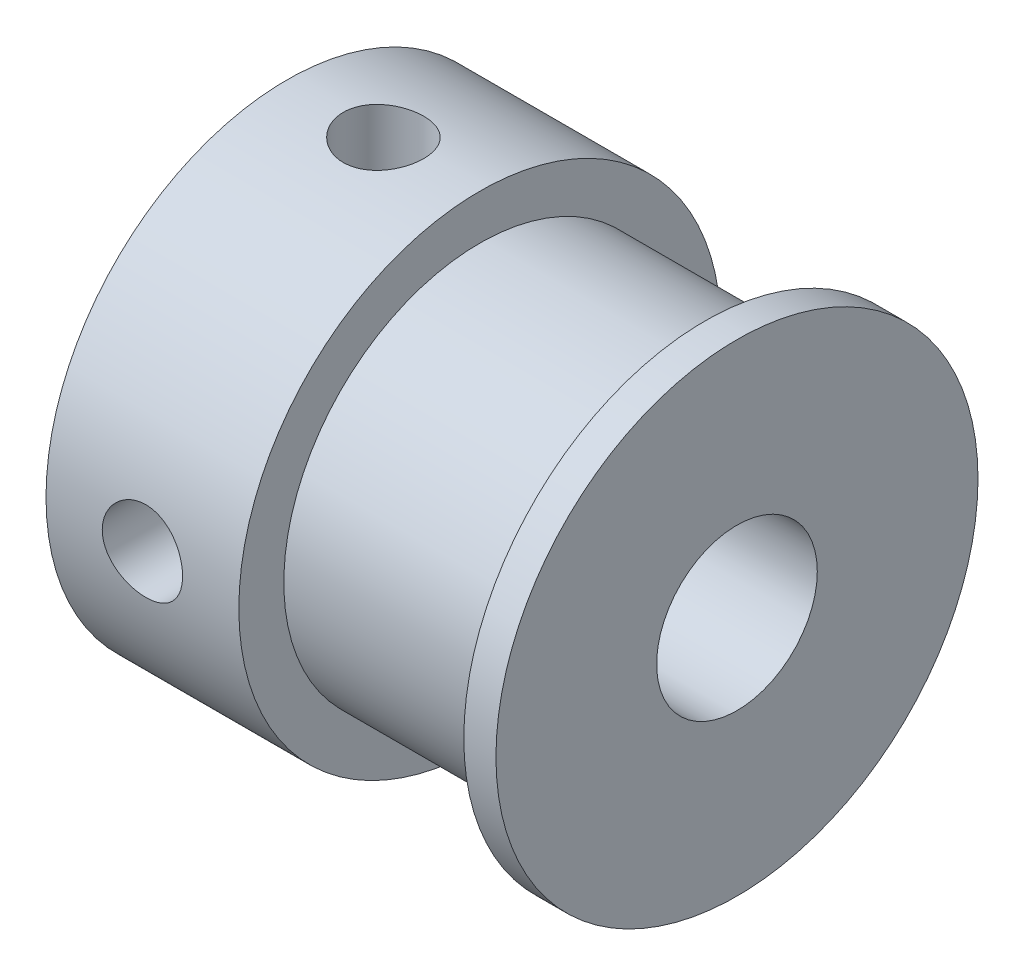
SolidWorks part; units mm, degrees
material "6061-T6 (SS)"
ref_plane "Front Plane" through (0, 0, 0) normal (0, 0, 1) x (1, 0, 0)
ref_plane "Top Plane" through (0, 0, 0) normal (0, 1, 0) x (1, 0, 0)
ref_plane "Right Plane" through (0, 0, 0) normal (1, 0, 0) x (0, 0, -1)
sketch "Sketch1" plane through (0, 0, 0) normal (0, 0, 1) x (1, 0, 0)
  line L0 (0, 2.5) -> (0, 7.5)
  line L1 (0, 7.5) -> (6, 7.5)
  line L2 (6, 7.5) -> (6, 6.1)
  line L3 (6, 6.1) -> (13, 6.1)
  line L4 (13, 6.1) -> (13, 7.5)
  line L5 (13, 7.5) -> (14, 7.5)
  line L6 (14, 7.5) -> (14, 2.5)
  line L7 (14, 2.5) -> (0, 2.5)
  line L8 (0, 0) -> (-7.6744, 0) construction
  dimension "D1" = 5
  dimension "D2" = 15
  dimension "D3" = 12.2
  dimension "D4" = 6
  dimension "D5" = 14
  dimension "D6" = 1
revolve "Revolve1" add sketch "Sketch1" angle 360 about L8
hole_wizard "M3x0.5 Tapped Hole1" positions "Sketch3" profile "Sketch2" tap size "M3x0.5" standard "ANSI Metric"
sketch "Sketch3" plane through (0, 0, 0) normal (0, 1, 0) x (1, 0, 0)
  line L0 (0, 0) -> (6, 0) construction
  line L1 (6, -6.1) -> (6, 6.1) construction
  point P8 (3, 0)
sketch "Sketch2" plane through (3, 0, 0) normal (1, 0, 0) x (0, 0, -1)
  line L0 (0, 0) -> (0, 7.5)
  line L1 (0, 7.5) -> (1.25, 7.5)
  line L2 (1.25, 7.5) -> (1.25, 0)
  line L5 (1.25, 0) -> (0, 0)
  line L11 (0, -6.35) -> (0, 107.95) construction
  dimension "Thread Major Dia." = 2.5
  dimension "Thru Tap Drill Depth" = 7.5
hole_wizard "M3x0.5 Tapped Hole2" positions "Sketch5" profile "Sketch4" tap size "M3x0.5" standard "ANSI Metric"
sketch "Sketch5" plane through (0, 0, 0) normal (0, 0, 1) x (1, 0, 0)
  line L0 (0, 0) -> (6, 0) construction
  line L1 (6, -6.1) -> (6, 6.1) construction
  point P7 (3, 0)
sketch "Sketch4" plane through (3, 0, 0) normal (1, 0, 0) x (0, 1, 0)
  line L0 (0, 0) -> (0, 7.5)
  line L1 (0, 7.5) -> (1.25, 7.5)
  line L2 (1.25, 7.5) -> (1.25, 0)
  line L5 (1.25, 0) -> (0, 0)
  line L11 (0, -6.35) -> (0, 107.95) construction
  dimension "Thread Major Dia." = 2.5
  dimension "Thru Tap Drill Depth" = 7.5
ref_plane "Plane1" through (9.5, 0, 0) normal (1, 0, 0) x (0, 0, -1)
